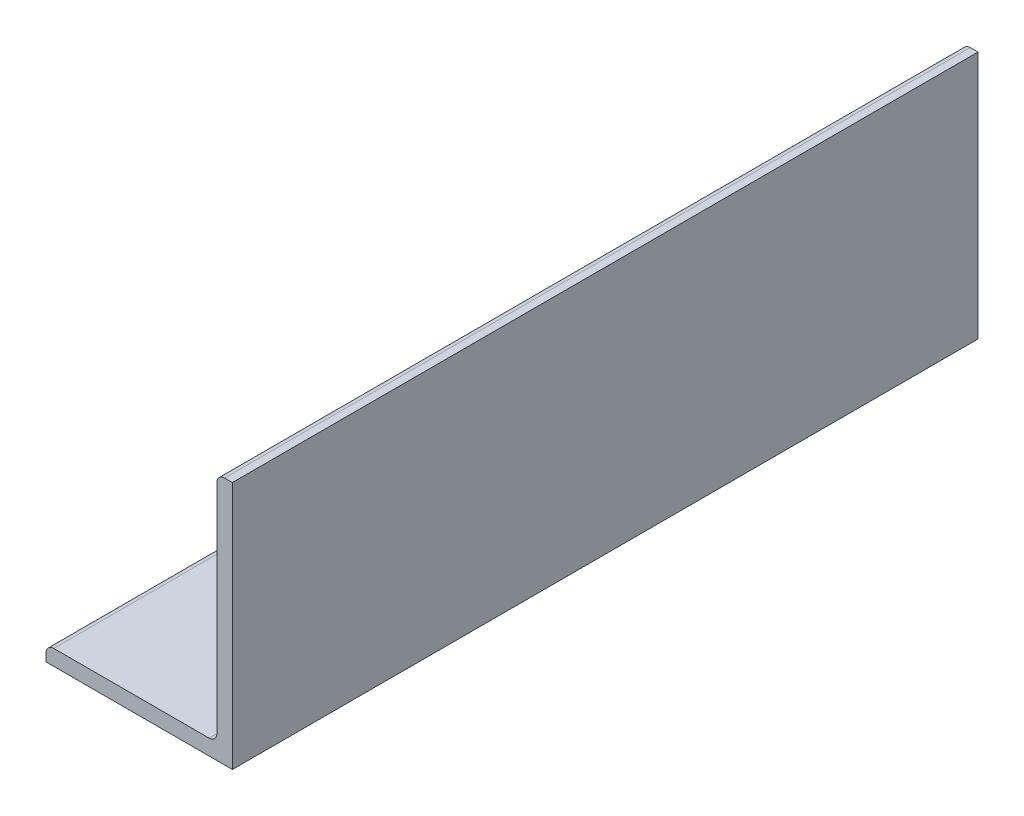
SolidWorks part; units mm, degrees
ref_plane "Front Plane" through (0, 0, 0) normal (0, 0, 1) x (1, 0, 0)
ref_plane "Top Plane" through (0, 0, 0) normal (0, 1, 0) x (1, 0, 0)
ref_plane "Right Plane" through (0, 0, 0) normal (1, 0, 0) x (0, 0, -1)
sketch "Sketch2" plane through (0, 0, 0) normal (0, 0, 1) x (1, 0, 0)
  line L0 (-38.1, 0) -> (38.1, 0)
  line L1 (38.1, 0) -> (38.1, 101.6)
  line L2 (38.1, 101.6) -> (31.75, 101.6) construction
  line L3 (31.75, 98.425) -> (31.75, 9.525)
  line L4 (28.575, 6.35) -> (-34.925, 6.35)
  line L5 (-38.1, 0) -> (-38.1, 6.35) construction
  line L6 (34.925, 101.6) -> (38.1, 101.6)
  line L7 (-38.1, 3.175) -> (-38.1, 0)
  arc A0 (31.75, 98.425) -> (34.925, 101.6) centre (34.925, 98.425) cw
  arc A1 (-38.1, 3.175) -> (-34.925, 6.35) centre (-34.925, 3.175) cw
  arc A2 (31.75, 9.525) -> (28.575, 6.35) centre (28.575, 9.525) cw
  dimension "Vert" = 101.6
  dimension "Horz" = 76.2
  dimension "Thickness" = 6.35
extrude "Boss-Extrude1" add sketch "Sketch2" along normal mid plane 304.8
ref_plane "Contact Plane 1" through (0, 6.35, 0) normal (0, 1, 0) x (1, 0, 0)
ref_plane "Contact Plane 2" through (31.75, 0, 0) normal (-1, 0, 0) x (0, 0, 1)
